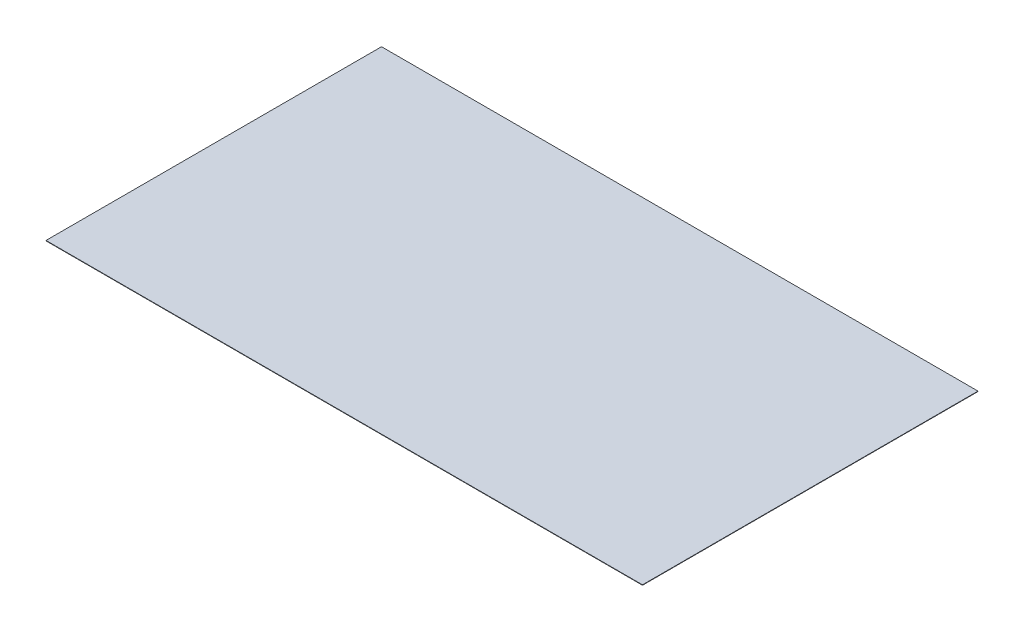
SolidWorks part; units mm, degrees
ref_plane "Front Plane" through (0, 0, 0) normal (0, 0, 1) x (1, 0, 0)
ref_plane "Top Plane" through (0, 0, 0) normal (0, 1, 0) x (1, 0, 0)
ref_plane "Right Plane" through (0, 0, 0) normal (1, 0, 0) x (0, 0, -1)
sketch "Sketch1" plane through (0, 0, 0) normal (0, 1, 0) x (1, 0, 0)
  line L1 (0, 0) -> (3657.6, 0)
  line L2 (0, 0) -> (0, -2057.4)
  line L3 (0, -2057.4) -> (3657.6, -2057.4)
  line L4 (3657.6, 0) -> (3657.6, -2057.4)
extrude "Boss-Extrude1" add sketch "Sketch1" along normal blind 2.54
